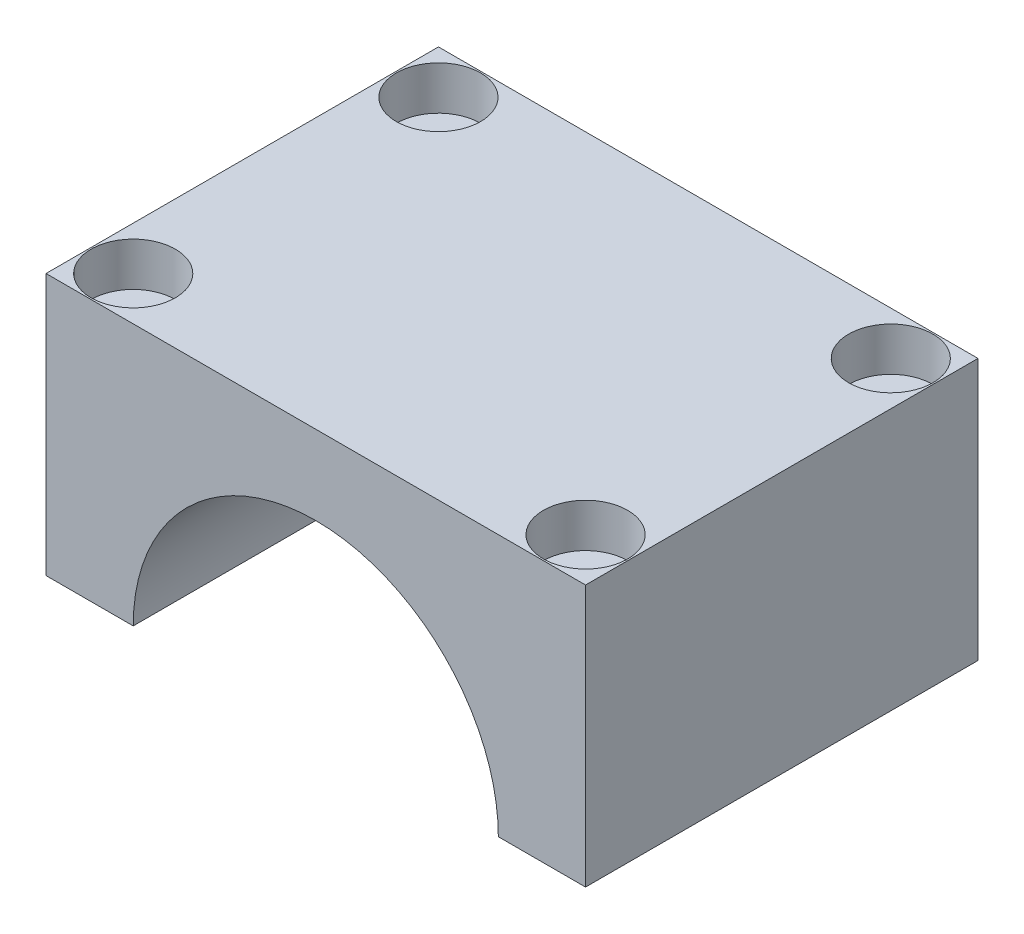
SolidWorks part; units mm, degrees
ref_plane "Plan de face" through (0, 0, 0) normal (0, 0, 1) x (1, 0, 0)
ref_plane "Plan de dessus" through (0, 0, 0) normal (0, 1, 0) x (1, 0, 0)
ref_plane "Plan de droite" through (0, 0, 0) normal (1, 0, 0) x (0, 0, -1)
sketch "Esquisse1" plane through (0, 0, 0) normal (0, 0, 1) x (1, 0, 0)
  line L0 (0, 0) -> (-84.6745, 0) construction
  line L1 (0, 0) -> (94.0931, 0) construction
  line L2 (-12.5601, 0) -> (-18.5601, 0)
  line L3 (0, 0) -> (0, 12.5601) construction
  line L4 (-18.5601, 0) -> (-18.5601, 18)
  line L5 (-18.5601, 18) -> (18.5601, 18)
  line L6 (18.5601, 0) -> (18.5601, 18)
  line L7 (12.5601, 0) -> (18.5601, 0)
  line L8 (0, 12.5601) -> (0, 18) construction
  arc A0 (-12.5601, 0) -> (12.5601, 0) centre (0, 0) cw
  point P11 (0, 18)
  dimension "D1" = 6
  dimension "D2" = 18
extrude "Boss.-Extru.1" add sketch "Esquisse1" along normal blind 27
sketch "Esquisse5" plane through (0, 18, 0) normal (0, 1, 0) x (1, 0, 0)
  line L0 (18.5601, -13.5) -> (-18.5601, -13.5) construction
  line L1 (18.5601, -27) -> (18.5601, 0) construction
  line L2 (-18.5601, -27) -> (-18.5601, 0) construction
  line L3 (0, 0) -> (0, -27) construction
  line L4 (18.5601, 0) -> (-18.5601, 0) construction
  line L5 (18.5601, -27) -> (-18.5601, -27) construction
  line L6 (15.5601, 0) -> (15.5601, -27) construction
  line L7 (18.5601, -3) -> (-18.5601, -3) construction
  line L8 (18.5601, 0) -> (18.5601, -27) construction
  line L9 (18.5601, -27) -> (-18.5601, -27) construction
  line L10 (-18.5601, -27) -> (-18.5601, 0) construction
  line L11 (-18.5601, 0) -> (18.5601, 0) construction
  circle A0 centre (15.5601, -3) radius 1.3
  circle A1 centre (15.5601, -24) radius 1.3
  circle A2 centre (-15.5601, -3) radius 1.3
  circle A3 centre (-15.5601, -24) radius 1.3
  dimension "D1" = 3
  dimension "D2" = 3
extrude "Enlèv. mat.-Extru.1" cut sketch "Esquisse5" against normal blind 18
sketch "Esquisse6" plane through (0, 18, 0) normal (0, 1, 0) x (1, 0, 0)
  line L0 (18.5601, -13.5) -> (-18.5601, -13.5) construction
  line L1 (0, 0) -> (0, -13.5) construction
  line L2 (15.5601, 0) -> (15.5601, -13.5) construction
  line L3 (18.5601, -3) -> (-18.2321, -3) construction
  line L4 (18.5601, -13.5) -> (18.5601, -27) construction
  line L5 (18.5601, -27) -> (-18.5601, -27) construction
  line L6 (-18.5601, -27) -> (-18.5601, -13.5) construction
  line L7 (-18.5601, -13.5) -> (18.5601, -13.5) construction
  line L8 (18.5601, -27) -> (18.5601, 0) construction
  line L9 (18.5601, 0) -> (-18.5601, 0) construction
  circle A0 centre (15.5601, -3) radius 2.9
  circle A1 centre (15.5601, -24) radius 2.9
  circle A2 centre (-15.5601, -3) radius 2.9
  circle A3 centre (-15.5601, -24) radius 2.9
  dimension "D1" = 3
  dimension "D2" = 3
extrude "Enlèv. mat.-Extru.2" cut sketch "Esquisse6" against normal blind 3
